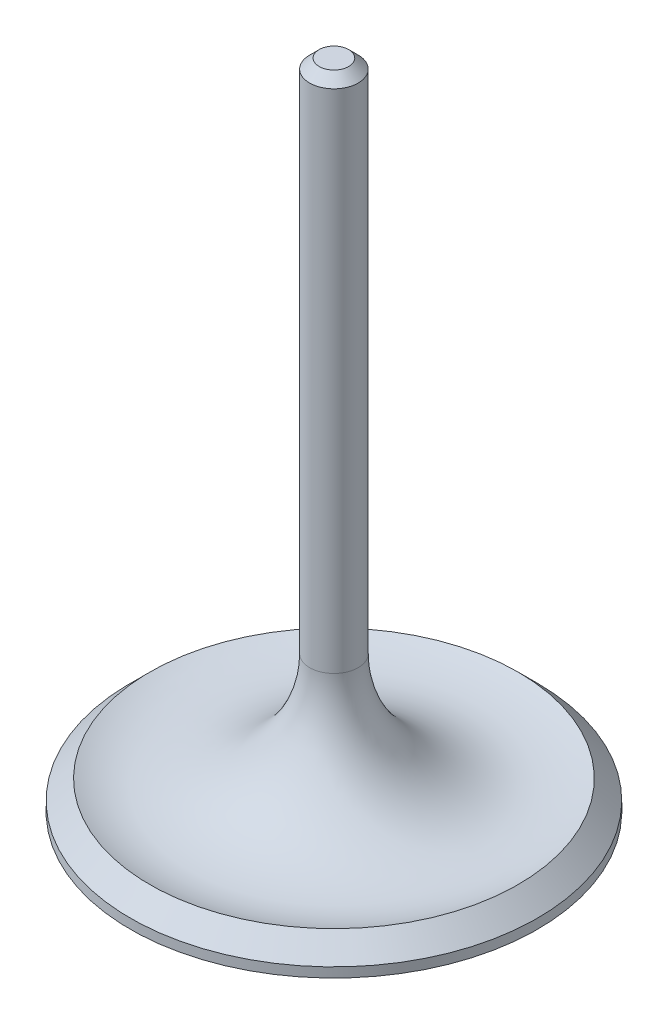
SolidWorks part; units mm, degrees
ref_plane "Alzado" through (0, 0, 0) normal (0, 0, 1) x (1, 0, 0)
ref_plane "Planta" through (0, 0, 0) normal (0, 1, 0) x (1, 0, 0)
ref_plane "Vista lateral" through (0, 0, 0) normal (1, 0, 0) x (0, 0, -1)
sketch "Croquis1" plane through (0, 0, 0) normal (1, 0, 0) x (0, 0, -1)
  line L0 (0, 0) -> (0, 85.55)
  line L1 (0, 85.55) -> (3.18, 85.55)
  line L2 (3.18, 85.55) -> (3.18, 17.9547)
  line L3 (24.13, 3.81) -> (26.67, 1.27)
  line L4 (26.67, 1.27) -> (26.67, 0)
  line L5 (26.67, 0) -> (0, 0)
  arc A0 (3.18, 17.9547) -> (24.13, 3.81) centre (18.43, 17.9547) ccw
  point P8 (0, 0)
  point P10 (0, 0)
  dimension "D1" = 85.55
  dimension "D7" = 15.25
  dimension "D2" = 26.67
  dimension "D3" = 3.18
  dimension "D4" = 1.27
  dimension "D5" = 3.81
  dimension "D6" = 45
revolve "Revolución1" add sketch "Croquis1" angle 360 about L0
chamfer "Chaflán1" distance 1.25 angle 45 1 edges at (0, 85.55, -3.18)
